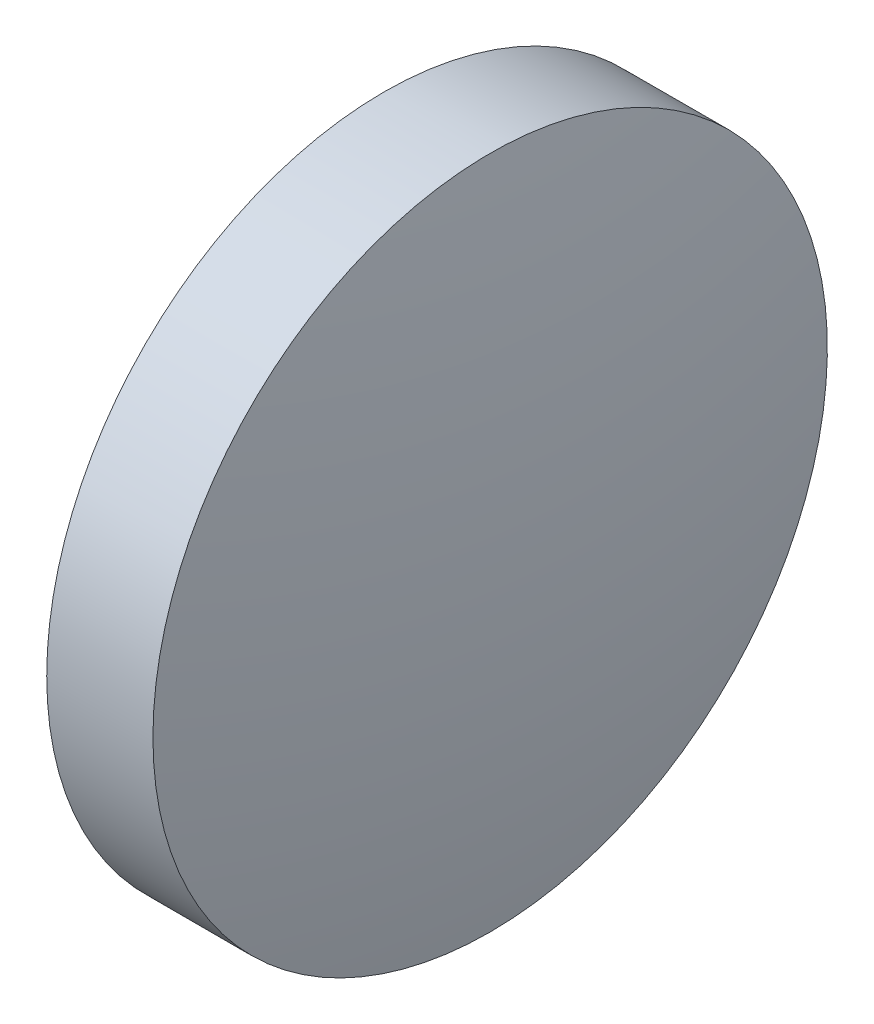
SolidWorks part; units mm, degrees
ref_plane "前视基准面" through (0, 0, 0) normal (0, 0, 1) x (1, 0, 0)
ref_plane "上视基准面" through (0, 0, 0) normal (0, 1, 0) x (1, 0, 0)
ref_plane "右视基准面" through (0, 0, 0) normal (1, 0, 0) x (0, 0, -1)
sketch "草图1" plane through (0, 0, 0) normal (0, 0, 1) x (1, 0, 0)
  line L0 (39.6527, 24.3081) -> (46.7386, 24.3081) construction
  line L1 (42.2291, 30.6581) -> (44.2291, 30.6581)
  line L2 (44.2291, 30.6581) -> (44.2291, 17.9581)
  line L3 (44.2291, 17.9581) -> (42.2291, 17.9581)
  line L4 (42.2291, 17.9581) -> (42.2291, 30.6581)
  arc A0 (42.2291, 30.6581) -> (42.2291, 17.9581) centre (75.5341, 24.3081) ccw
  arc A1 (44.2291, 17.9581) -> (44.2291, 30.6581) centre (10.9241, 24.3081) ccw
  dimension "D1" = 12.7
  dimension "D2" = 2.0001
revolve "旋转1" add sketch "草图1" angle 360 about L0
